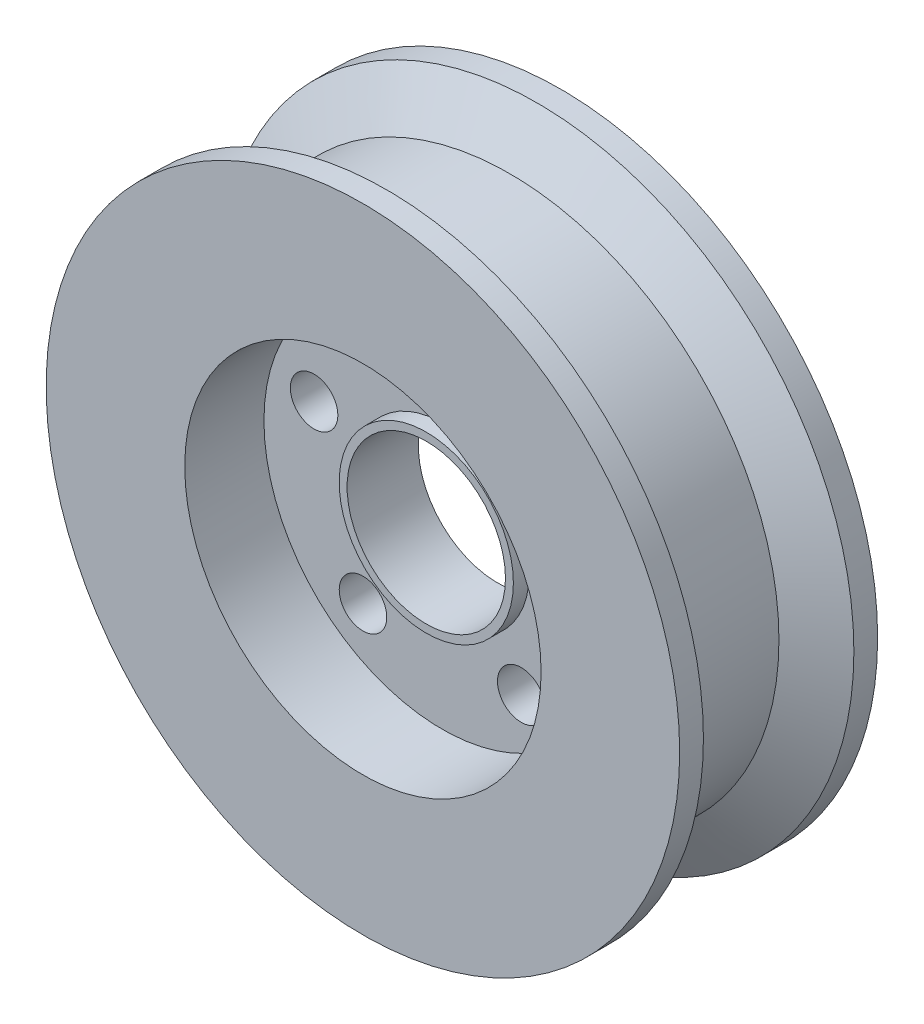
SolidWorks part; units mm, degrees
ref_plane "Front Plane" through (0, 0, 0) normal (0, 0, 1) x (1, 0, 0)
ref_plane "Top Plane" through (0, 0, 0) normal (0, 1, 0) x (1, 0, 0)
ref_plane "Right Plane" through (0, 0, 0) normal (1, 0, 0) x (0, 0, -1)
sketch "Sketch1" plane through (0, 0, 0) normal (0, 0, 1) x (1, 0, 0)
  circle A0 centre (0, 0) radius 40
  circle A1 centre (0, 0) radius 10
  dimension "D1" = 20
  dimension "D2" = 80
extrude "Boss-Extrude1" add sketch "Sketch1" along normal mid plane 25
sketch "Sketch2" plane through (0, 0, 12.5) normal (0, 0, 1) x (1, 0, 0)
  circle A0 centre (0, 0) radius 22.5
  circle A2 centre (0, 0) radius 40 construction
  dimension "D1" = 17.5
extrude "Cut-Extrude1" cut sketch "Sketch2" against normal blind 10
mirror "Mirror1" about plane through (0, 0, 0) normal (0, 0, 1) of "Cut-Extrude1"
sketch "Sketch3" plane through (0, 0, 2.5) normal (0, 0, 1) x (1, 0, 0)
  circle A0 centre (0, 17) radius 3
  dimension "D1" = 6
  dimension "D2" = 17
extrude "Cut-Extrude2" cut sketch "Sketch3" against normal through all
pattern_circular "CirPattern1" count 5 over 360 about axis through (0, 0, 0) along (0, 0, 1) of "Cut-Extrude2"
sketch "Sketch4" plane through (0, 0, 2.5) normal (0, 0, 1) x (1, 0, 0)
  circle A0 centre (0, 0) radius 11
  circle A1 centre (0, 0) radius 10 construction
  circle A2 centre (0, 0) radius 10
  dimension "D1" = 22
extrude "Boss-Extrude2" add sketch "Sketch4" along normal blind 2 and the other way blind 7
sketch "Sketch5" plane through (0, 0, 0) normal (0, 1, 0) x (1, 0, 0)
  line L0 (0, 0) -> (0, 27.7225) construction
  line L1 (-40, 9.5) -> (-34, 6.0359)
  line L2 (-40, 12.5) -> (-40, -12.5) construction
  line L3 (-34, 6.0359) -> (-34, -6.0359)
  line L4 (-34, -6.0359) -> (-40, -9.5)
  line L5 (-40, -9.5) -> (-40, 9.5)
  dimension "D1" = 3
  dimension "D2" = 3
  dimension "D3" = 6
  dimension "D4" = 60
  dimension "D5" = 60
revolve "Cut-Revolve1" cut sketch "Sketch5" angle 360 about L0
